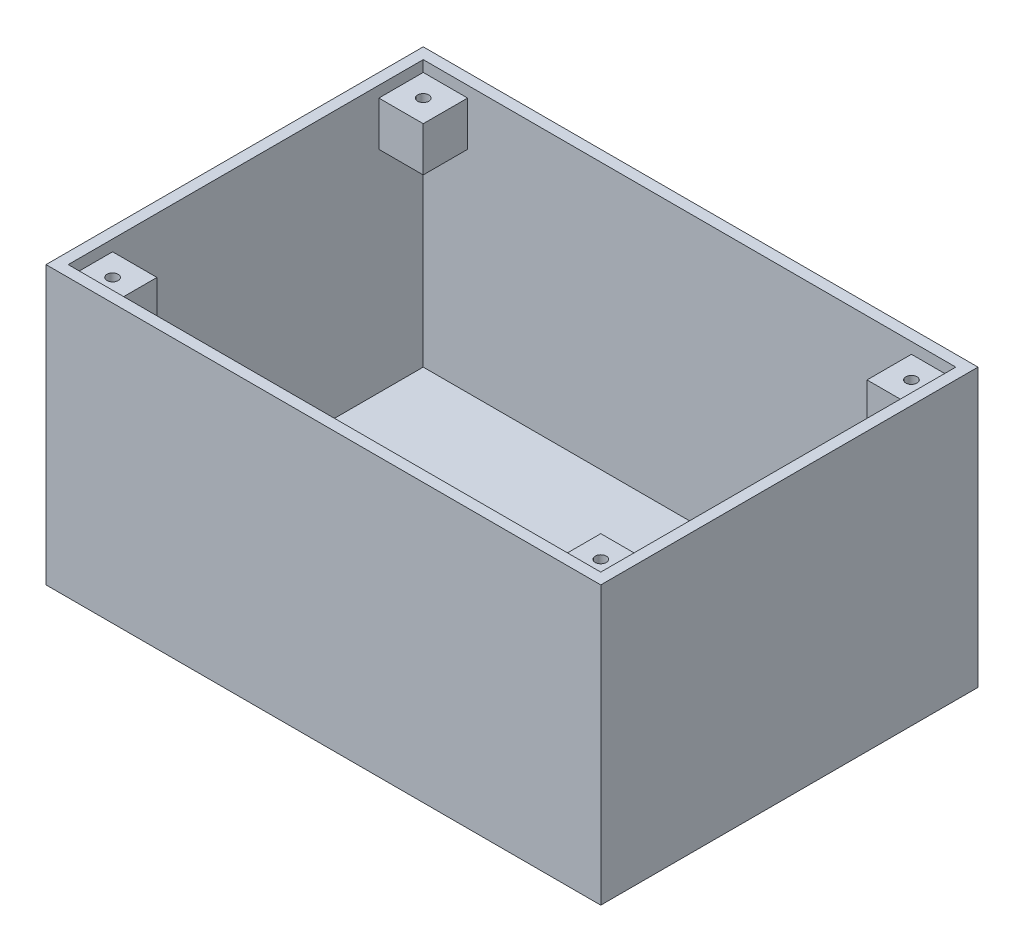
SolidWorks part; units mm, degrees
ref_plane "Front Plane" through (0, 0, 0) normal (0, 0, 1) x (1, 0, 0)
ref_plane "Top Plane" through (0, 0, 0) normal (0, 1, 0) x (1, 0, 0)
ref_plane "Right Plane" through (0, 0, 0) normal (1, 0, 0) x (0, 0, -1)
sketch "Sketch1" plane through (0, 0, 0) normal (0, 1, 0) x (1, 0, 0)
  line L1 (158.75, -107.95) -> (-158.75, -107.95)
  line L2 (158.75, -107.95) -> (158.75, 107.95)
  line L3 (158.75, 107.95) -> (-158.75, 107.95)
  line L4 (-158.75, -107.95) -> (-158.75, 107.95)
  line L5 (158.75, -107.95) -> (-158.75, 107.95) construction
  line L6 (158.75, 107.95) -> (-158.75, -107.95) construction
  point P0 (0, 0)
  dimension "D1" = 317.5
  dimension "D2" = 215.9
extrude "Boss-Extrude1" add sketch "Sketch1" along normal blind 6.35
sketch "Sketch2" plane through (0, 6.35, 0) normal (0, 1, 0) x (1, 0, 0)
  line L0 (158.75, 107.95) -> (-158.75, 107.95) construction
  line L1 (152.4, -101.6) -> (-152.4, -101.6)
  line L2 (152.4, -101.6) -> (152.4, 101.6)
  line L3 (152.4, 101.6) -> (-152.4, 101.6)
  line L4 (-152.4, -101.6) -> (-152.4, 101.6)
  line L5 (152.4, -101.6) -> (-152.4, 101.6) construction
  line L6 (152.4, 101.6) -> (-152.4, -101.6) construction
  line L7 (-158.75, 107.95) -> (-158.75, -107.95) construction
  line L12 (-158.75, 107.95) -> (-158.75, -107.95)
  line L13 (-158.75, -107.95) -> (158.75, -107.95)
  line L14 (158.75, -107.95) -> (158.75, 107.95)
  line L15 (158.75, 107.95) -> (-158.75, 107.95)
  line L16 (-158.75, 107.95) -> (-158.75, -107.95)
  line L17 (-158.75, -107.95) -> (158.75, -107.95)
  line L18 (158.75, -107.95) -> (158.75, 107.95)
  line L19 (158.75, 107.95) -> (-158.75, 107.95)
  point P0 (0, 0)
  point P12 (-152.4, 101.6)
  dimension "D1" = 6.35
  dimension "D2" = 6.35
  dimension "D3" = 0
extrude "Boss-Extrude2" add sketch "Sketch2" along normal blind 152.4
sketch "Sketch3" plane through (0, 0, -101.6) normal (0, 0, 1) x (1, 0, 0)
  line L0 (152.4, 158.75) -> (-152.4, 158.75) construction
  line L1 (-152.4, 152.4) -> (-127, 152.4)
  line L2 (-152.4, 152.4) -> (-152.4, 127)
  line L3 (-152.4, 127) -> (-127, 127)
  line L4 (-127, 152.4) -> (-127, 127)
  line L5 (-152.4, 158.75) -> (-152.4, 6.35) construction
  line L6 (0, 6.35) -> (0, 158.75) construction
  line L7 (152.4, 6.35) -> (-152.4, 6.35) construction
  line L8 (152.4, 127) -> (127, 127)
  line L9 (127, 152.4) -> (127, 127)
  line L10 (152.4, 152.4) -> (127, 152.4)
  line L11 (152.4, 152.4) -> (152.4, 127)
  dimension "D1" = 25.4
  dimension "D2" = 25.4
  dimension "D3" = 6.35
extrude "Boss-Extrude3" add sketch "Sketch3" along normal blind 25.4 separate body
sketch "Sketch5" plane through (0, 0, 101.6) normal (0, 0, -1) x (-1, 0, 0)
  line L0 (-152.4, 158.75) -> (-152.4, 6.35) construction
  line L1 (-152.4, 152.4) -> (-127, 152.4)
  line L2 (-152.4, 152.4) -> (-152.4, 127)
  line L3 (-152.4, 127) -> (-127, 127)
  line L4 (-127, 152.4) -> (-127, 127)
  line L5 (152.4, 158.75) -> (-152.4, 158.75) construction
  line L6 (0, 6.35) -> (0, 158.75) construction
  line L7 (152.4, 6.35) -> (-152.4, 6.35) construction
  line L8 (152.4, 127) -> (127, 127)
  line L9 (127, 152.4) -> (127, 127)
  line L10 (152.4, 152.4) -> (127, 152.4)
  line L11 (152.4, 152.4) -> (152.4, 127)
  dimension "D1" = 6.35
  dimension "D2" = 25.4
  dimension "D3" = 25.4
extrude "Boss-Extrude5" add sketch "Sketch5" along normal blind 25.4 separate body
sketch "Sketch6" plane through (0, 152.4, 0) normal (0, 1, 0) x (1, 0, 0)
  line L0 (152.4, -101.6) -> (127, -76.2) construction
  line L1 (-119.5982, 0) -> (119.5982, 0) construction
  line L2 (0, 69.4729) -> (0, -69.4729) construction
  circle A0 centre (139.7, -88.9) radius 3.175
  circle A1 centre (-139.7, -88.9) radius 3.175
  circle A2 centre (-139.7, 88.9) radius 3.175
  circle A3 centre (139.7, 88.9) radius 3.175
  point P10 (0, 0)
  point P14 (0, 0)
  dimension "D1" = 6.35
extrude "Cut-Extrude1" cut sketch "Sketch6" against normal blind 15.24
